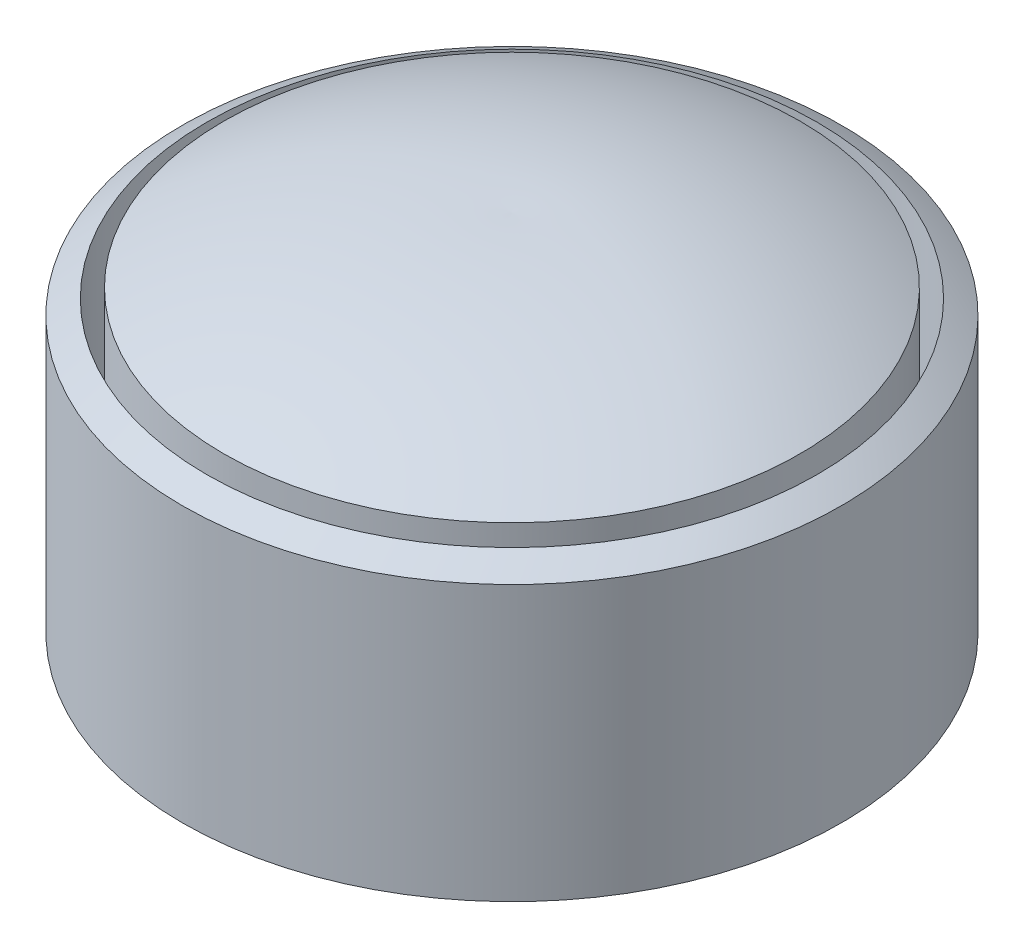
SolidWorks part; units mm, degrees
ref_plane "Front Plane" through (0, 0, 0) normal (0, 0, 1) x (1, 0, 0)
ref_plane "Top Plane" through (0, 0, 0) normal (0, 1, 0) x (1, 0, 0)
ref_plane "Right Plane" through (0, 0, 0) normal (1, 0, 0) x (0, 0, -1)
sketch "Sketch1" plane through (0, 0, 0) normal (0, 0, 1) x (1, 0, 0)
  line L0 (0, 0) -> (0, 4)
  line L1 (0, 0) -> (4.8, 0)
  line L2 (4.8, 5.3) -> (4.8, 0)
  spline S0 degree 2 poles (0, 4) (2.1841, 5.3976) (4.8, 5.3) knots 0 0 0 1 1 1
  dimension "D1" = 4.8
  dimension "D2" = 4
  dimension "D3" = 5.3
revolve "Revolve1" add sketch "Sketch1" angle 360 about L2
sketch "Sketch2" plane through (0, 0, 0) normal (0, -1, 0) x (1, 0, 0)
  circle A0 centre (4.8, 0) radius 4.4454
  circle A1 centre (4.8, 0) radius 4.1967
extrude "Cut-Extrude1" cut sketch "Sketch2" against normal blind 4.5
